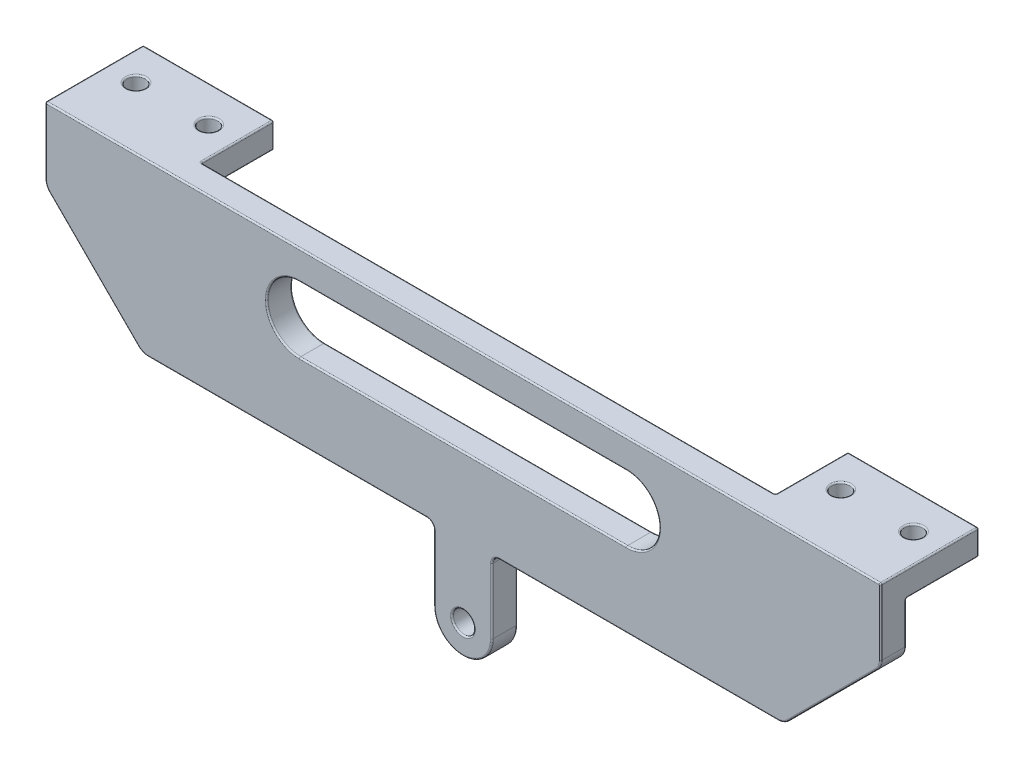
SolidWorks part; units mm, degrees
ref_plane "Front Plane" through (0, 0, 0) normal (0, 0, 1) x (1, 0, 0)
ref_plane "Top Plane" through (0, 0, 0) normal (0, 1, 0) x (1, 0, 0)
ref_plane "Right Plane" through (0, 0, 0) normal (1, 0, 0) x (0, 0, -1)
sketch "Sketch1" plane through (0, 0, 0) normal (0, 0, 1) x (1, 0, 0)
  line L0 (-100, 0) -> (100, 0) construction
  line L1 (-100, 0) -> (0, 100) construction
  line L2 (0, 100) -> (100, 0) construction
  line L3 (0, 0) -> (-50, 50) construction
  line L4 (-40, 60) -> (40, 60) construction
  line L5 (0, 100) -> (0, 60) construction
  circle A0 centre (-100, 0) radius 20
  circle A1 centre (0, 0) radius 20
  circle A2 centre (100, 0) radius 20
  point P2 (0, 0)
  dimension "D5" = 40
  dimension "D1" = 200
  dimension "D2" = 90
  dimension "D3" = 90
  dimension "D4" = 80
sketch "Sketch2" plane through (0, 0, 0) normal (0, 0, 1) x (1, 0, 0)
  line L0 (93.636, 20.5061) -> (79.4939, 6.364)
  line L1 (90.9809, 17.8509) -> (104.534, 4.6576)
  line L2 (-57.0711, 42.9289) -> (-40, 60) construction
  line L3 (-100, 0) -> (0, 100) construction
  line L4 (-40, 60) -> (40, 60) construction
  line L5 (40, 60) -> (86.565, 13.435) construction
  line L6 (0, 100) -> (100, 0) construction
  line L7 (-50, 35.8579) -> (-35.8579, 50)
  line L8 (-35.8579, 50) -> (35.8579, 50)
  line L9 (35.8579, 50) -> (79.4939, 6.364)
  line L10 (-64.1421, 50) -> (-44.1421, 70)
  line L11 (-44.1421, 70) -> (44.1421, 70)
  line L12 (44.1421, 70) -> (93.636, 20.5061)
  line L13 (-64.1421, 50) -> (-50, 35.8579)
  line L14 (82.1491, 9.0191) -> (95.3424, -4.534)
  line L15 (90.1005, 24.0416) -> (75.9584, 9.8995) construction
  line L17 (0, 100) -> (0, 60) construction
  line L18 (6, 70) -> (3.4304, 82.6944)
  line L19 (-6, 70) -> (-3.4304, 82.6944)
  circle A0 centre (100, 0) radius 3.5
  circle A1 centre (100, 0) radius 10 construction
  arc A2 (95.3424, -4.534) -> (104.534, 4.6576) centre (100, 0) ccw
  circle A3 centre (100, 0) radius 20 construction
  circle A4 centre (100, 0) radius 6.5 construction
  circle A5 centre (86.565, 20.5061) radius 1
  circle A6 centre (79.4939, 13.435) radius 1
  circle A7 centre (0, 60) radius 1.5
  circle A9 centre (0, 82) radius 1.5
  arc A10 (3.4304, 82.6944) -> (-3.4304, 82.6944) centre (0, 82) ccw
  circle A11 centre (0, 82) radius 3.5 construction
  circle A13 centre (-50, 50) radius 1.5
  dimension "D4" = 20
  dimension "D5" = 7
  dimension "D9" = 2
  dimension "D12" = 3
  dimension "D18" = 3
  dimension "D3" = 20
  dimension "D7" = 19
  dimension "D8" = 5
  dimension "D10" = 5
  dimension "D11" = 5
  dimension "D13" = 12
  dimension "D15" = 6
  dimension "D16" = 6
  dimension "D1" = 10
  dimension "D2" = 10
  dimension "D6" = 3
  dimension "D14" = 2
sketch "Sketch3" plane through (0, 0, 0) normal (0, 0, 1) x (1, 0, 0)
  line L0 (-86.565, 13.435) -> (-50, 50) construction
  line L1 (-100, 0) -> (0, 100) construction
  line L2 (-50, 50) -> (-13.435, 13.435) construction
  line L3 (0, 0) -> (-50, 50) construction
  line L4 (-79.4939, 6.364) -> (-50, 35.8579)
  line L5 (-50, 35.8579) -> (-20.5061, 6.364)
  line L6 (-93.636, 20.5061) -> (-50, 64.1421)
  line L7 (-50, 64.1421) -> (-6.364, 20.5061)
  line L8 (-79.4939, 6.364) -> (-50, 35.8579) construction
  line L9 (-93.636, 20.5061) -> (-50, 64.1421) construction
  line L10 (-93.636, 20.5061) -> (-79.4939, 6.364)
  line L11 (-6.364, 20.5061) -> (-20.5061, 6.364)
  line L12 (-104.534, 4.6576) -> (-90.9809, 17.8509)
  line L13 (-95.4038, -4.5962) -> (-81.9688, 8.8388)
  line L14 (4.5962, 4.5962) -> (-8.8388, 18.0312)
  line L15 (-4.5962, -4.5962) -> (-18.0312, 8.8388)
  line L16 (-90.1005, 24.0416) -> (-75.9584, 9.8995) construction
  line L17 (-9.8995, 24.0416) -> (-24.0416, 9.8995) construction
  circle A0 centre (-100, 0) radius 3.5
  circle A1 centre (0, 0) radius 3.5
  circle A2 centre (-100, 0) radius 10 construction
  circle A3 centre (0, 0) radius 10 construction
  arc A4 (-104.534, 4.6576) -> (-95.4038, -4.5962) centre (-100, 0) ccw
  arc A5 (-4.5962, -4.5962) -> (4.5962, 4.5962) centre (0, 0) ccw
  circle A6 centre (-100, 0) radius 20 construction
  circle A7 centre (-100, 0) radius 6.5 construction
  circle A8 centre (0, 0) radius 6.5 construction
  circle A9 centre (-86.565, 20.5061) radius 1
  circle A10 centre (-79.4939, 13.435) radius 1
  circle A11 centre (-20.5061, 13.435) radius 1
  circle A12 centre (-13.435, 20.5061) radius 1
  circle A13 centre (-50, 50) radius 1.5 construction
  circle A14 centre (-50, 50) radius 1.5
  dimension "D1" = 7
  dimension "D2" = 20
  dimension "D3" = 3
  dimension "D8" = 2
  dimension "D6" = 19
  dimension "D7" = 19
  dimension "D9" = 5
  dimension "D10" = 5
  dimension "D11" = 5
  dimension "D12" = 5
  dimension "D13" = 5
  dimension "D14" = 5
  dimension "D4" = 10
  dimension "D5" = 10
sketch "Sketch5" plane through (0, 0, 0) normal (0, 0, 1) x (1, 0, 0)
  line L6 (4, 60) -> (4, 70)
  line L7 (-4, 60) -> (-4, 70)
  line L10 (-57.5, 93.3579) -> (57.5, 93.3579)
  line L11 (57.5, 93.3579) -> (57.5, 83.3579)
  line L12 (57.5, 83.3579) -> (44.1421, 70)
  line L13 (44.1421, 70) -> (-44.1421, 70)
  line L14 (-44.1421, 70) -> (-57.5, 83.3579)
  line L15 (-57.5, 83.3579) -> (-57.5, 93.3579)
  line L16 (-22.5, 84.8579) -> (22.5, 84.8579) construction
  line L17 (-22.5, 89.3579) -> (22.5, 89.3579)
  line L18 (-22.5, 80.3579) -> (22.5, 80.3579)
  circle A0 centre (0, 60) radius 1.5 construction
  circle A1 centre (0, 60) radius 1.5
  arc A2 (-4, 60) -> (4, 60) centre (0, 60) ccw
  circle A3 centre (0, 60) radius 4 construction
  arc A4 (-22.5, 89.3579) -> (-22.5, 80.3579) centre (-22.5, 84.8579) ccw
  arc A5 (22.5, 80.3579) -> (22.5, 89.3579) centre (22.5, 84.8579) ccw
  point P2 (0, 93.3579)
  point P7 (0, 84.8579)
  dimension "D1" = 115
  dimension "D2" = 10
  dimension "D3" = 2.5
  dimension "D4" = 45
  dimension "D5" = 9
  dimension "D6" = 4
sketch "Sketch6" plane through (0, 0, 0) normal (0, 0, 1) x (1, 0, 0)
  line L0 (-4, 60) -> (-4, 70) construction
  line L1 (4, 60) -> (4, 70) construction
  line L2 (-22.5, 80.3579) -> (22.5, 80.3579)
  line L3 (22.5, 89.3579) -> (-22.5, 89.3579)
  line L4 (-22.5, 80.3579) -> (22.5, 80.3579)
  line L5 (22.5, 89.3579) -> (-22.5, 89.3579)
  line L6 (57.5, 93.3579) -> (-57.5, 93.3579)
  line L7 (57.5, 83.3579) -> (57.5, 93.3579)
  line L8 (44.1421, 70) -> (57.5, 83.3579)
  line L9 (-44.1421, 70) -> (44.1421, 70)
  line L10 (-57.5, 83.3579) -> (-44.1421, 70)
  line L11 (-57.5, 93.3579) -> (-57.5, 83.3579)
  line L12 (57.5, 93.3579) -> (-57.5, 93.3579)
  line L13 (57.5, 83.3579) -> (57.5, 93.3579)
  line L14 (44.1421, 70) -> (57.5, 83.3579)
  line L15 (-44.1421, 70) -> (-4, 70)
  line L16 (-57.5, 83.3579) -> (-44.1421, 70)
  line L17 (-57.5, 93.3579) -> (-57.5, 83.3579)
  line L18 (-4, 60) -> (-4, 70)
  line L19 (4, 60) -> (4, 70)
  line L20 (4, 70) -> (44.1421, 70)
  arc A0 (-4, 60) -> (4, 60) centre (0, 60) ccw construction
  circle A1 centre (0, 60) radius 1.5
  circle A2 centre (0, 60) radius 1.5
  arc A3 (-4, 60) -> (4, 60) centre (0, 60) ccw
  arc A4 (22.5, 80.3579) -> (22.5, 89.3579) centre (22.5, 84.8579) ccw
  arc A5 (-22.5, 89.3579) -> (-22.5, 80.3579) centre (-22.5, 84.8579) ccw
  arc A6 (22.5, 80.3579) -> (22.5, 89.3579) centre (22.5, 84.8579) ccw
  arc A7 (-22.5, 89.3579) -> (-22.5, 80.3579) centre (-22.5, 84.8579) ccw
  dimension "D1" = 0
  dimension "D2" = 0
  dimension "D3" = 0
extrude "Boss-Extrude1" add sketch "Sketch6" along normal blind 3.5
sketch "Sketch7" plane through (0, 93.3579, 0) normal (0, 1, 0) x (1, 0, 0)
  line L0 (-57.5, 0) -> (-39.5, 0)
  line L1 (57.5, 0) -> (-57.5, 0) construction
  line L2 (-39.5, 0) -> (-39.5, 10)
  line L3 (-39.5, 10) -> (-57.5, 10)
  line L4 (-57.5, 10) -> (-57.5, 0)
  line L5 (-57.5, 5) -> (-39.5, 5) construction
  line L6 (-48.5, 5) -> (-48.5, 10) construction
  line L7 (0, 0) -> (0, 22.0812) construction
  line L8 (48.5, 5) -> (48.5, 10) construction
  line L9 (57.5, 5) -> (39.5, 5) construction
  line L10 (57.5, 10) -> (57.5, 0)
  line L11 (39.5, 10) -> (57.5, 10)
  line L12 (39.5, 0) -> (39.5, 10)
  line L13 (57.5, 0) -> (39.5, 0)
  circle A0 centre (-53.5, 5) radius 1.25
  circle A1 centre (-43.5, 5) radius 1.25
  circle A2 centre (43.5, 5) radius 1.25
  circle A3 centre (53.5, 5) radius 1.25
  dimension "D4" = 2.5
  dimension "D1" = 18
  dimension "D2" = 10
  dimension "D3" = 10
extrude "Boss-Extrude2" add sketch "Sketch7" against normal blind 3.5
fillet "Fillet1" radius 2 4 edges at (44.1421, 70, 1.75) (57.5, 83.3579, 1.75) (-44.1421, 70, 1.75) (-57.5, 83.3579, 1.75)
fillet "Fillet2" radius 1 2 edges at (-4, 70, 1.75) (4, 70, 1.75)
fillet "Fillet3" radius 0.2 70 edges at (57.5, 91.6079, -10) (39.5, 91.6079, 0) (39.5, 91.6079, -10) (57.5, 89.8579, -5) (48.5, 89.8579, 0) (39.5, 89.8579, -5) (48.5, 89.8579, -10) (39.5, 93.3579, -5) (48.5, 93.3579, -10) (43.5, 89.8579, -6.25) (43.5, 93.3579, -6.25) (53.5, 89.8579, -6.25) (53.5, 93.3579, -6.25) (-43.5, 93.3579, -3.75) (-43.5, 89.8579, -3.75) (-53.5, 93.3579, -3.75) (-53.5, 89.8579, -3.75) (-39.5, 93.3579, -5) (-48.5, 93.3579, -10) (-57.5, 89.8579, -5) (-48.5, 89.8579, 0) (-39.5, 89.8579, -5) (-48.5, 89.8579, -10) (-39.5, 91.6079, 0) (-39.5, 91.6079, -10) (-57.5, 91.6079, -10) (27, 84.8579, 0) (0, 89.3579, 0) (0, 80.3579, 0) (27, 84.8579, 3.5) (0, 89.3579, 3.5) (-27, 84.8579, 3.5) (0, 80.3579, 3.5) (1.5, 60, 0) (1.5, 60, 3.5) (-57.5, 87.0221, 0) (-50.8211, 76.6789, 0) (-24.1569, 70, 0) (-4, 64.5, 0) (0, 56, 0) (4, 64.5, 0) (24.1569, 70, 0) (50.8211, 76.6789, 0) (57.5, 87.0221, 0) (0, 93.3579, 0) (-57.5, 88.7721, 3.5) (-50.8211, 76.6789, 3.5) (-24.1569, 70, 3.5) (-4, 64.5, 3.5) (0, 56, 3.5) (4, 64.5, 3.5) (24.1569, 70, 3.5) (50.8211, 76.6789, 3.5) (57.5, 88.7721, 3.5) (0, 93.3579, 3.5) (-57.5, 93.3579, -3.25) (57.5, 93.3579, -3.25) (-57.3478, 83.4209, 0) (-44.0791, 70.1522, 0) (57.3478, 83.4209, 0) (44.0791, 70.1522, 0) (-57.3478, 83.4209, 3.5) (-44.0791, 70.1522, 3.5) (57.3478, 83.4209, 3.5) (44.0791, 70.1522, 3.5) (-4.2929, 69.7071, 0) (-4.2929, 69.7071, 3.5) (4.2929, 69.7071, 0) (4.2929, 69.7071, 3.5) (-27, 84.8579, 0)
